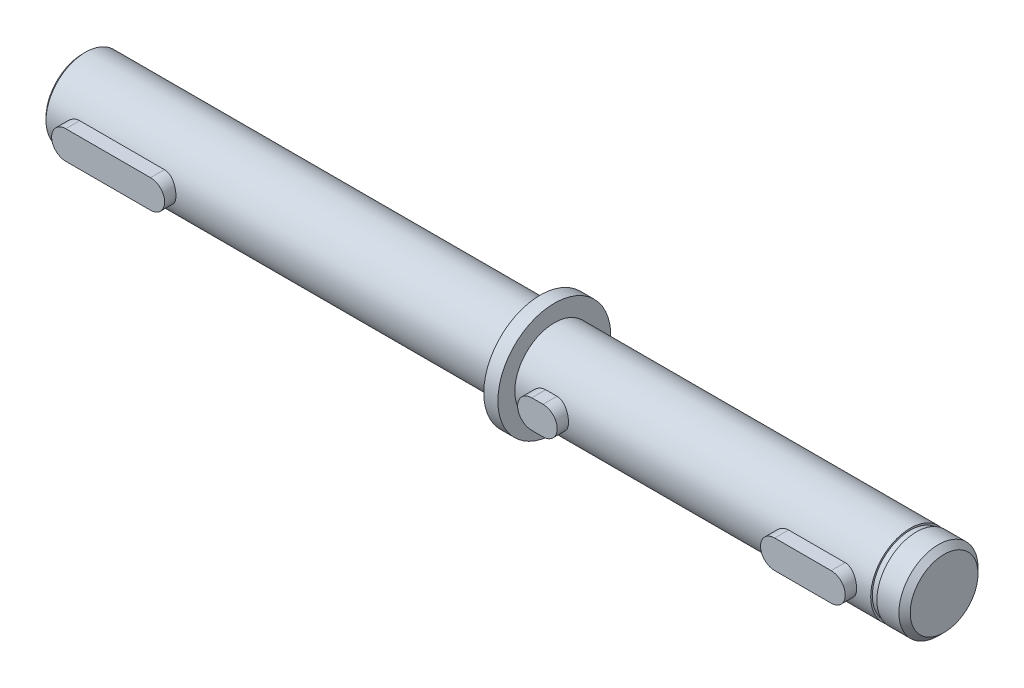
SolidWorks part; units mm, degrees
material "铸造合金钢"
ref_plane "前视基准面" through (0, 0, 0) normal (0, 0, 1) x (1, 0, 0)
ref_plane "上视基准面" through (0, 0, 0) normal (0, 1, 0) x (1, 0, 0)
ref_plane "右视基准面" through (0, 0, 0) normal (1, 0, 0) x (0, 0, -1)
sketch "草图1" plane through (0, 0, 0) normal (0, 0, 1) x (1, 0, 0)
  line L1 (-89.5, 0) -> (89.5, 0)
  line L2 (-89.5, 0) -> (-89.5, 6.5)
  line L3 (-89, 7) -> (-8.5, 7)
  line L4 (-8.5, 7) -> (-8.5, 10)
  line L5 (-8.5, 10) -> (-6, 10)
  line L6 (-6, 10) -> (-6, 7)
  line L7 (89.5, 6) -> (88.5, 7)
  line L13 (-89.5, 6.5) -> (-89, 7)
  line L16 (88.5, 7) -> (-6, 7)
  line L17 (89.5, 0) -> (89.5, 6)
  point P6 (-89.5, 7)
  point P13 (89.5, 7)
  dimension "D1" = 83.5
  dimension "D2" = 81
  dimension "D3" = 7
  dimension "D4" = 179
  dimension "D5" = 7
  dimension "D6" = 10
revolve "旋转1" add sketch "草图1" angle 360 about L1
sketch "草图2" plane through (0, 0, 0) normal (0, 0, 1) x (1, 0, 0)
  line L0 (83.5, 0) -> (68.5, 0) construction
  line L1 (83.5, -2.5) -> (68.5, -2.5)
  line L2 (83.5, 2.5) -> (68.5, 2.5)
  line L3 (0, 0) -> (0, 28.608) construction
  line L4 (89.5, -6) -> (89.5, 6) construction
  line L5 (-83.5, 0) -> (-68.5, 0) construction
  line L6 (-83.5, -2.5) -> (-68.5, -2.5)
  line L7 (-83.5, 2.5) -> (-68.5, 2.5)
  line L8 (-1, 0) -> (9, 0) construction
  line L9 (-1, 2.5) -> (9, 2.5)
  line L10 (-1, -2.5) -> (9, -2.5)
  line L11 (-6, -7) -> (-6, 7) construction
  line L12 (83.5, 0) -> (68.5, 0) construction
  line L13 (83.5, -2.5) -> (68.5, -2.5)
  line L14 (83.5, 2.5) -> (68.5, 2.5)
  line L15 (1, 0) -> (-9, 0) construction
  line L16 (1, 2.5) -> (-9, 2.5)
  line L17 (1, -2.5) -> (-9, -2.5)
  line L18 (42, 0) -> (52, 0) construction
  line L19 (42, 2.5) -> (52, 2.5)
  line L20 (42, -2.5) -> (52, -2.5)
  arc A0 (83.5, -2.5) -> (83.5, 2.5) centre (83.5, 0) ccw
  arc A1 (68.5, 2.5) -> (68.5, -2.5) centre (68.5, 0) ccw
  arc A2 (-83.5, -2.5) -> (-83.5, 2.5) centre (-83.5, 0) cw
  arc A3 (-68.5, 2.5) -> (-68.5, -2.5) centre (-68.5, 0) cw
  arc A4 (-1, 2.5) -> (-1, -2.5) centre (-1, 0) ccw
  arc A5 (9, -2.5) -> (9, 2.5) centre (9, 0) ccw
  arc A6 (83.5, -2.5) -> (83.5, 2.5) centre (83.5, 0) ccw
  arc A7 (68.5, 2.5) -> (68.5, -2.5) centre (68.5, 0) ccw
  arc A8 (1, 2.5) -> (1, -2.5) centre (1, 0) cw
  arc A9 (-9, -2.5) -> (-9, 2.5) centre (-9, 0) cw
  arc A10 (42, 2.5) -> (42, -2.5) centre (42, 0) ccw
  arc A11 (52, -2.5) -> (52, 2.5) centre (52, 0) ccw
  point P3 (76, 0)
  point P14 (-76, 0)
  point P21 (4, 0)
  point P36 (-4, 0)
  point P41 (47, 0)
  dimension "D1" = 2.5
  dimension "D4" = 2.5
  dimension "D8" = 2.5
  dimension "D2" = 6
  dimension "D3" = 15
  dimension "D5" = 10
  dimension "D6" = 5
  dimension "D7" = 10
  dimension "D9" = 33
extrude "凸台-拉伸1" add sketch "草图2" along normal blind 9 contours A3 L7 A2 L6 | L10 A5 L9 A4 | L2 A1 L1 A0 | L20 A11 L19 A10
sketch "草图3" plane through (89.5, 0, 0) normal (1, 0, 0) x (0, 0, -1)
  circle A0 centre (0, 0) radius 15
  dimension "D1" = 30
extrude "切除-拉伸1" cut sketch "草图3" against normal blind 26.5
hole_wizard "M6 螺纹孔1" positions "草图5" profile "草图4" tap size "M6" standard "GB"
sketch "草图5" plane through (-89.5, 0, 0) normal (-1, 0, 0) x (0, 0, 1)
  point P0 (0, 0)
sketch "草图4" plane through (-89.5, 0, 0) normal (0, 1, 0) x (0, 0, 1)
  line L0 (0, 0) -> (0, 18.5022)
  line L1 (0, 18.5022) -> (2.5, 17)
  line L2 (2.5, 17) -> (2.5, 0)
  line L5 (2.5, 0) -> (0, 0)
  line L10 (0, 18.5022) -> (-2.5, 17) construction
  line L11 (0, -6.35) -> (0, 107.95) construction
  dimension "螺纹孔钻头直径" = 5
  dimension "螺纹孔钻头深度" = 17
  dimension "导头角度" = 118
cosmetic thread "孔螺蚊线1" parameters "D1"=12, "D2"=6
chamfer "倒角1" distance 1 angle 45 1 edges at (63, 0, -7)
sketch "草图6" plane through (0, 0, 0) normal (0, 0, 1) x (1, 0, 0)
  line L0 (0, 0) -> (40.44, 0) construction
  line L1 (-6, -7) -> (62, -7) construction
  line L2 (57, -7) -> (58.1, -7)
  line L3 (57, -7) -> (57, -6.7)
  line L4 (57, -6.7) -> (58.1, -6.7)
  line L5 (58.1, -7) -> (58.1, -6.7)
  line L6 (-6, -7) -> (-6, 7) construction
  dimension "D1" = 63
  dimension "D2" = 1.1
  dimension "D3" = 13.4
revolve "切除-旋转1" cut sketch "草图6" angle 360 about L0
